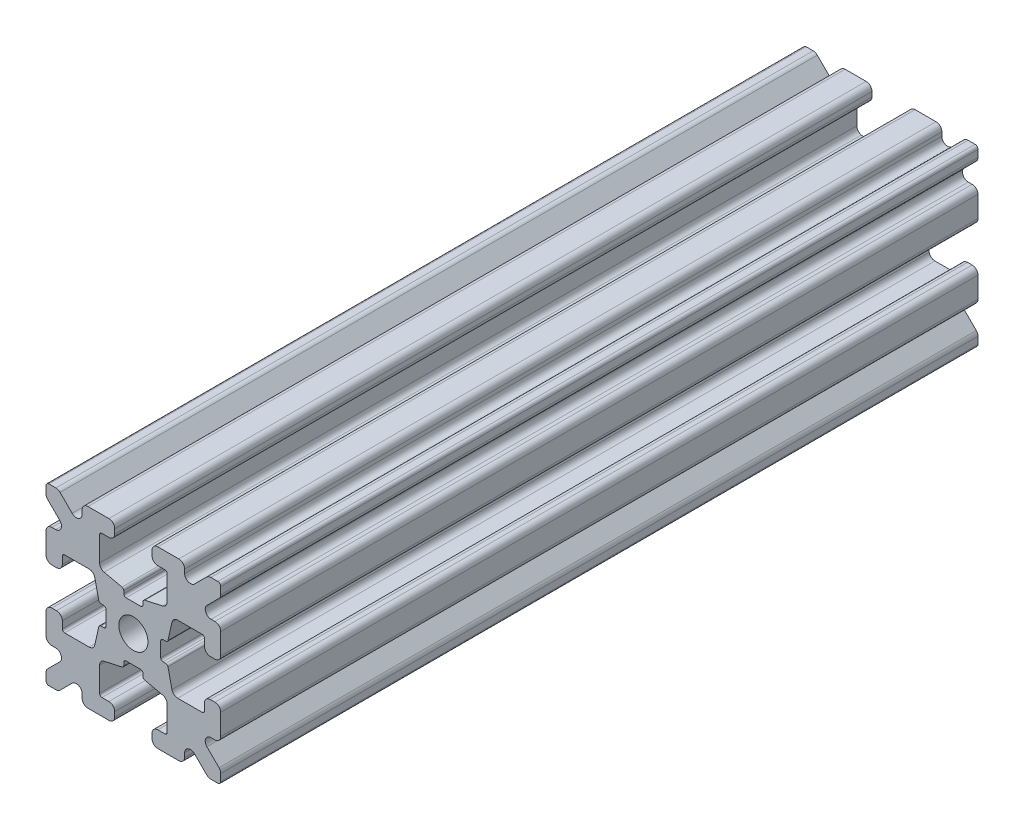
SolidWorks part; units mm, degrees
ref_plane "Front Plane" through (0, 0, 0) normal (0, 0, 1) x (1, 0, 0)
ref_plane "Top Plane" through (0, 0, 0) normal (0, 1, 0) x (1, 0, 0)
ref_plane "Right Plane" through (0, 0, 0) normal (1, 0, 0) x (0, 0, -1)
sketch "Sketch1" plane through (0, 0, 0) normal (0, 0, 1) x (1, 0, 0)
  line L1 (-7.5, -7.5) -> (7.5, -7.5)
  line L2 (-7.5, -7.5) -> (-7.5, 7.5)
  line L3 (-7.5, 7.5) -> (7.5, 7.5)
  line L4 (7.5, -7.5) -> (7.5, 7.5)
  line L5 (-7.5, -7.5) -> (7.5, 7.5) construction
  line L6 (-7.5, 7.5) -> (7.5, -7.5) construction
  circle A0 centre (0, 0) radius 1.25
  point P0 (0, 0)
  dimension "D2" = 2.5
  dimension "D1" = 15
extrude "Boss-Extrude1" add sketch "Sketch1" along normal mid plane 65
fillet "Fillet1" radius 0.25 4 edges at (7.5, -7.5, 0) (-7.5, -7.5, 0) (7.5, 7.5, 0) (-7.5, 7.5, 0)
sketch "Sketch2" plane through (0, 0, 32.5) normal (0, 0, 1) x (1, 0, 0)
  line L0 (-7.5, 7.25) -> (-7.5, -7.25) construction
  line L1 (-7.5, 1.6) -> (-6.1, 1.6)
  line L2 (-7.5, 1.6) -> (-7.5, -1.6)
  line L3 (-7.5, -1.6) -> (-6.1, -1.6)
  line L4 (-6.1, 1.6) -> (-6.1, 2.9)
  line L5 (0, 0) -> (-12.1036, 0) construction
  line L6 (-6.1, -2.9) -> (-3.4, -2.9)
  line L7 (0, 0) -> (-7.25, 7.25) construction
  line L8 (-6.1, 2.9) -> (-3.4, 2.9)
  line L9 (-3.4, -2.9) -> (-3.4, 2.9)
  line L10 (55, 0) -> (-55, 0) construction
  line L11 (-6.1, -2.9) -> (-6.1, -1.6)
  line L12 (2.9, 6.1) -> (1.6, 6.1)
  line L13 (2.9, 3.4) -> (-2.9, 3.4)
  line L14 (-2.9, 6.1) -> (-2.9, 3.4)
  line L15 (2.9, 6.1) -> (2.9, 3.4)
  line L16 (-1.6, 6.1) -> (-2.9, 6.1)
  line L17 (1.6, 7.5) -> (1.6, 6.1)
  line L18 (-1.6, 7.5) -> (1.6, 7.5)
  line L19 (-1.6, 7.5) -> (-1.6, 6.1)
  line L20 (-1.6, -7.5) -> (-1.6, -6.1)
  line L21 (-1.6, -7.5) -> (1.6, -7.5)
  line L22 (1.6, -7.5) -> (1.6, -6.1)
  line L23 (-1.6, -6.1) -> (-2.9, -6.1)
  line L24 (2.9, -6.1) -> (2.9, -3.4)
  line L25 (-2.9, -6.1) -> (-2.9, -3.4)
  line L26 (2.9, -3.4) -> (-2.9, -3.4)
  line L27 (2.9, -6.1) -> (1.6, -6.1)
  line L28 (6.1, -2.9) -> (6.1, -1.6)
  line L29 (3.4, -2.9) -> (3.4, 2.9)
  line L30 (6.1, 2.9) -> (3.4, 2.9)
  line L31 (6.1, -2.9) -> (3.4, -2.9)
  line L32 (6.1, 1.6) -> (6.1, 2.9)
  line L33 (7.5, -1.6) -> (6.1, -1.6)
  line L34 (7.5, 1.6) -> (7.5, -1.6)
  line L35 (7.5, 1.6) -> (6.1, 1.6)
  dimension "D1" = 3.2
  dimension "D2" = 5.8
  dimension "D3" = 1.4
  dimension "D4" = 2.7
extrude "Cut-Extrude1" cut sketch "Sketch2" against normal through all
sketch "Sketch4" plane through (0, 0, 32.5) normal (0, 0, 1) x (1, 0, 0)
  line L0 (-3.4, 2.9) -> (-2.75, 0)
  line L1 (55, 0) -> (-55, 0) construction
  line L2 (-2.75, 0) -> (-3.4, -2.9)
  line L3 (-3.4, -2.9) -> (-3.4, 2.9) construction
  line L4 (-3.4, 2.9) -> (-3.4, -2.9)
  line L5 (-2.9, 3.4) -> (0, 2.75)
  line L6 (0, 2.75) -> (2.9, 3.4)
  line L7 (2.9, 3.4) -> (-2.9, 3.4)
  line L8 (3.4, 2.9) -> (2.75, 0)
  line L9 (2.75, 0) -> (3.4, -2.9)
  line L10 (3.4, -2.9) -> (3.4, 2.9)
  line L11 (-2.9, -3.4) -> (0, -2.75)
  line L12 (0, -2.75) -> (2.9, -3.4)
  line L13 (2.9, -3.4) -> (-2.9, -3.4)
  circle A2 centre (0, 0) radius 2.75
  circle A3 centre (0, 0) radius 2.75 construction
  dimension "D1" = 1.5
extrude "Cut-Extrude3" cut sketch "Sketch4" against normal through all
fillet "Fillet3" radius 0.5 16 edges at (-6.1, -1.6, 0) (-7.5, -1.6, 0) (-6.1, 1.6, 0) (-7.5, 1.6, 0) (-1.6, -7.5, 0) (-1.6, -6.1, 0) (1.6, -7.5, 0) (1.6, -6.1, 0) (6.1, -1.6, 0) (7.5, -1.6, 0) (7.5, 1.6, 0) (6.1, 1.6, 0) (1.6, 7.5, 0) (1.6, 6.1, 0) (-1.6, 7.5, 0) (-1.6, 6.1, 0)
fillet "Fillet4" radius 0.5 8 edges at (-3.4, 2.9, 0) (-3.4, -2.9, 0) (2.9, -3.4, 0) (-2.9, -3.4, 0) (3.4, -2.9, 0) (3.4, 2.9, 0) (-2.9, 3.4, 0) (2.9, 3.4, 0)
fillet "Fillet5" radius 3 4 edges at (0, -2.75, 0) (2.75, 0, 0) (-2.75, 0, 0) (0, 2.75, 0)
fillet "Fillet6" radius 0.2 8 edges at (-2.9, -6.1, 0) (2.9, -6.1, 0) (6.1, -2.9, 0) (6.1, 2.9, 0) (2.9, 6.1, 0) (-2.9, 6.1, 0) (-6.1, -2.9, 0) (-6.1, 2.9, 0)
sketch "Sketch5" plane through (0, 0, 32.5) normal (0, 0, 1) x (1, 0, 0)
  line L0 (0, 0) -> (-7.25, 7.25) construction
  line L1 (-7.5, 6.4393) -> (-5.4607, 4.4)
  line L2 (-6.4393, 7.5) -> (-4.4, 5.4607)
  line L3 (-7.5, 4.4) -> (-5.4607, 4.4)
  line L4 (-3.8003, 2.9) -> (-5.9, 2.9) construction
  line L5 (0, 0) -> (-12.1819, 0) construction
  line L6 (-4.4, 7.5) -> (-4.4, 5.4607)
  line L7 (-2.9, 5.9) -> (-2.9, 3.8003) construction
  line L8 (-7.5, 6.4393) -> (-7.5, 4.4)
  line L9 (-7.5, 7.25) -> (-7.5, 2.1) construction
  line L10 (2.1, -7.5) -> (7.25, -7.5) construction
  line L11 (7.5, -7.25) -> (7.5, -2.1) construction
  line L12 (7.25, 7.5) -> (2.1, 7.5) construction
  line L13 (-2.1, 7.5) -> (-7.25, 7.5) construction
  line L14 (-4.4, 7.5) -> (-6.4393, 7.5)
  line L16 (55, 0) -> (-55, 0) construction
  line L17 (0, 0) -> (0, 10.993) construction
  line L18 (0, -54.6431) -> (0, 54.6431) construction
  line L20 (4.4, 7.5) -> (6.4393, 7.5)
  line L22 (7.5, 6.4393) -> (7.5, 4.4)
  line L23 (4.4, 7.5) -> (4.4, 5.4607)
  line L24 (7.5, 4.4) -> (5.4607, 4.4)
  line L25 (6.4393, 7.5) -> (4.4, 5.4607)
  line L26 (7.5, 6.4393) -> (5.4607, 4.4)
  line L27 (7.5, -6.4393) -> (5.4607, -4.4)
  line L28 (6.4393, -7.5) -> (4.4, -5.4607)
  line L29 (7.5, -4.4) -> (5.4607, -4.4)
  line L30 (4.4, -7.5) -> (4.4, -5.4607)
  line L31 (7.5, -6.4393) -> (7.5, -4.4)
  line L33 (4.4, -7.5) -> (6.4393, -7.5)
  line L36 (-4.4, -7.5) -> (-6.4393, -7.5)
  line L38 (-7.5, -6.4393) -> (-7.5, -4.4)
  line L39 (-4.4, -7.5) -> (-4.4, -5.4607)
  line L40 (-7.5, -4.4) -> (-5.4607, -4.4)
  line L41 (-6.4393, -7.5) -> (-4.4, -5.4607)
  line L42 (-7.5, -6.4393) -> (-5.4607, -4.4)
  dimension "D1" = 1.5
  dimension "D2" = 1.5
  dimension "D3" = 1.5
extrude "Cut-Extrude4" cut sketch "Sketch5" against normal through all
fillet "Fillet8" radius 0.5 24 edges at (-5.4607, 4.4, 0) (-7.5, 4.4, 0) (-5.4607, -4.4, 0) (-7.5, -4.4, 0) (-4.4, -7.5, 0) (-4.4, -5.4607, 0) (4.4, -7.5, 0) (4.4, -5.4607, 0) (5.4607, -4.4, 0) (7.5, -4.4, 0) (7.5, 4.4, 0) (5.4607, 4.4, 0) (4.4, 5.4607, 0) (4.4, 7.5, 0) (-4.4, 5.4607, 0) (-4.4, 7.5, 0) (-6.4393, 7.5, 0) (-7.5, 6.4393, 0) (6.4393, 7.5, 0) (7.5, 6.4393, 0) (6.4393, -7.5, 0) (7.5, -6.4393, 0) (-6.4393, -7.5, 0) (-7.5, -6.4393, 0)
sketch "Sketch6" plane through (0, 0, 32.5) normal (0, 0, 1) x (1, 0, 0)
  line L0 (0, 0) -> (0, 11.013) construction
  line L1 (0.6561, 2.8971) -> (2.1235, 2.8971) construction
  line L2 (0, -54.6431) -> (0, 54.6431) construction
  line L3 (0, 0) -> (7.25, 7.25) construction
  line L4 (7.5, 0.8255) -> (7.5, -0.8255)
  line L5 (2.3471, 0.8255) -> (7.5, 0.8255)
  line L6 (0, 0) -> (12.4016, 0) construction
  line L7 (0.8255, -7.5) -> (-0.8255, -7.5)
  line L8 (2.3471, -0.8255) -> (2.3471, 0.8255)
  line L9 (0.8255, -2.3471) -> (0.8255, -7.5)
  line L10 (7.5, -0.8255) -> (2.3471, -0.8255)
  line L11 (-7.5, -0.8255) -> (-2.3471, -0.8255)
  line L12 (-2.3471, -0.8255) -> (-2.3471, 0.8255)
  line L13 (-0.8255, -2.3471) -> (0.8255, -2.3471)
  line L14 (-0.8255, 7.5) -> (-0.8255, 2.3471)
  line L15 (-0.8255, 2.3471) -> (0.8255, 2.3471)
  line L16 (-0.8255, -7.5) -> (-0.8255, -2.3471)
  line L17 (0.8255, 2.3471) -> (0.8255, 7.5)
  line L18 (0.8255, 7.5) -> (-0.8255, 7.5)
  line L19 (3.9, 7.5) -> (2.1, 7.5) construction
  line L20 (-2.3471, 0.8255) -> (-7.5, 0.8255)
  line L21 (-7.5, 0.8255) -> (-7.5, -0.8255)
  point P5 (0, -2.5973)
  point P7 (0, 2.5973)
  dimension "D3" = 0.55
  dimension "D1" = 1.651
extrude "Cut-Extrude5" cut sketch "Sketch6" against normal through all
fillet "Fillet10" radius 0.2 16 edges at (-2.935, 0.8255, 0) (-2.935, -0.8255, 0) (2.935, -0.8255, 0) (2.935, 0.8255, 0) (0.8255, 2.935, 0) (-0.8255, 2.935, 0) (-2.3471, 0.8255, 0) (-2.3471, -0.8255, 0) (0.8255, 2.3471, 0) (-0.8255, 2.3471, 0) (2.3471, 0.8255, 0) (2.3471, -0.8255, 0) (0.8255, -2.935, 0) (0.8255, -2.3471, 0) (-0.8255, -2.3471, 0) (-0.8255, -2.935, 0)
